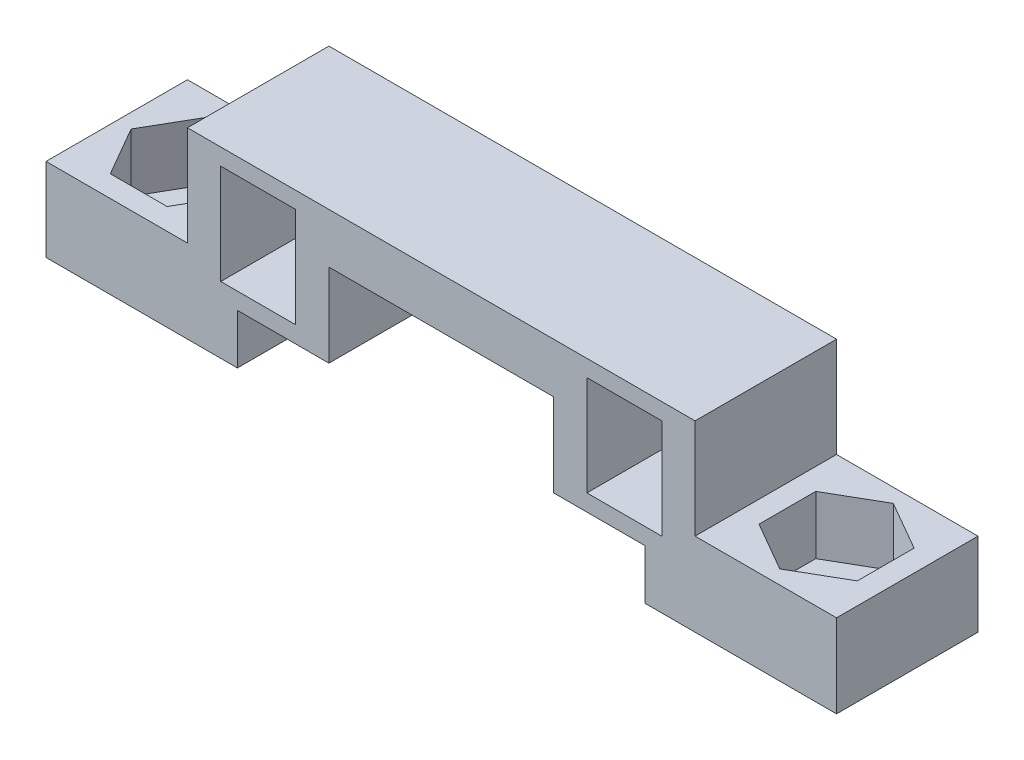
SolidWorks part; units mm, degrees
ref_plane "Front Plane" through (0, 0, 0) normal (0, 0, 1) x (1, 0, 0)
ref_plane "Top Plane" through (0, 0, 0) normal (0, 1, 0) x (1, 0, 0)
ref_plane "Right Plane" through (0, 0, 0) normal (1, 0, 0) x (0, 0, -1)
sketch "Sketch1" plane through (0, 0, 0) normal (0, 1, 0) x (1, 0, 0)
  line L1 (0, 0) -> (8.5, 0)
  line L2 (0, 0) -> (0, 8.5)
  line L3 (0, 8.5) -> (8.5, 8.5)
  line L4 (8.5, 0) -> (8.5, 8.5)
  line L5 (5.9855, 7.196) -> (2.5755, 7.196)
  line L6 (2.5755, 7.196) -> (0.8705, 4.2428)
  line L7 (0.8705, 4.2428) -> (2.5755, 1.2897)
  line L8 (2.5755, 1.2897) -> (5.9855, 1.2897)
  line L9 (5.9855, 1.2897) -> (7.6905, 4.2428)
  line L10 (7.6905, 4.2428) -> (5.9855, 7.196)
  circle A0 centre (4.2805, 4.2428) radius 2.9531 construction
  dimension "D1" = 8.5
  dimension "D2" = 8.5
  dimension "D3" = 3.41
extrude "Boss-Extrude1" add sketch "Sketch1" along normal blind 3.5
sketch "Sketch2" plane through (0, 0, 0) normal (0, -1, 0) x (1, 0, 0)
  line L1 (0, 0) -> (8.5, 0)
  line L2 (0, 0) -> (0, -8.5)
  line L3 (0, -8.5) -> (8.5, -8.5)
  line L4 (8.5, 0) -> (8.5, -8.5)
  circle A0 centre (4.25, -4.25) radius 1.5
  dimension "D1" = 3
extrude "Boss-Extrude2" add sketch "Sketch2" along normal blind 1.5
sketch "Sketch3" plane through (8.5, 0, 0) normal (1, 0, 0) x (0, 0, -1)
  line L1 (0, 3.5) -> (8.5, 3.5)
  line L2 (0, 3.5) -> (0, -1.5)
  line L3 (0, -1.5) -> (8.5, -1.5)
  line L4 (8.5, 3.5) -> (8.5, -1.5)
extrude "Boss-Extrude3" add sketch "Sketch3" along normal blind 3
sketch "Sketch4" plane through (0, 3.5, 0) normal (0, 1, 0) x (1, 0, 0)
  line L0 (0, 0) -> (11.5, 0) construction
  line L1 (11.5, 8.5) -> (8.5, 8.5)
  line L2 (11.5, 8.5) -> (11.5, 0)
  line L3 (11.5, 0) -> (8.5, 0)
  line L4 (8.5, 8.5) -> (8.5, 0)
  dimension "D1" = 3
extrude "Boss-Extrude4" add sketch "Sketch4" along normal blind 6
sketch "Sketch5" plane through (11.5, 0, 0) normal (1, 0, 0) x (0, 0, -1)
  line L0 (8.5, -1.5) -> (8.5, 9.5) construction
  line L1 (0, 9.5) -> (8.5, 9.5)
  line L2 (0, 9.5) -> (0, 6.5)
  line L3 (0, 6.5) -> (8.5, 6.5)
  line L4 (8.5, 9.5) -> (8.5, 6.5)
  dimension "D1" = 3
extrude "Boss-Extrude5" add sketch "Sketch5" along normal blind 27.5
sketch "Sketch6" plane through (0, 6.5, 0) normal (0, -1, 0) x (1, 0, 0)
  line L0 (39, -8.5) -> (11.5, -8.5) construction
  line L1 (39, 0) -> (36, 0)
  line L2 (39, 0) -> (39, -8.5)
  line L3 (39, -8.5) -> (36, -8.5)
  line L4 (36, 0) -> (36, -8.5)
  dimension "D1" = 3
extrude "Boss-Extrude6" add sketch "Sketch6" along normal up to surface (8 mm away) up to face at (5.75, -1.5, -4.25)
sketch "Sketch7" plane through (39, 0, 0) normal (1, 0, 0) x (0, 0, -1)
  line L0 (8.5, -1.5) -> (8.5, 9.5) construction
  line L1 (0, -1.5) -> (8.5, -1.5)
  line L2 (0, -1.5) -> (0, 3.5)
  line L3 (0, 3.5) -> (8.5, 3.5)
  line L4 (8.5, -1.5) -> (8.5, 3.5)
  dimension "D1" = 5
extrude "Boss-Extrude7" add sketch "Sketch7" along normal blind 8.5
sketch "Sketch8" plane through (0, 3.5, 0) normal (0, 1, 0) x (1, 0, 0)
  line L0 (39, 8.5) -> (39, 0) construction
  line L1 (46.2031, 5.955) -> (43.25, 7.66)
  line L2 (43.25, 7.66) -> (40.2969, 5.955)
  line L3 (40.2969, 5.955) -> (40.2969, 2.545)
  line L4 (40.2969, 2.545) -> (43.25, 0.84)
  line L5 (43.25, 0.84) -> (46.2031, 2.545)
  line L6 (46.2031, 2.545) -> (46.2031, 5.955)
  line L11 (47.5, 4.25) -> (39, 4.25) construction
  line L12 (47.5, 8.5) -> (47.5, 0) construction
  line L13 (43.25, 0) -> (43.25, 8.5) construction
  line L14 (47.5, 0) -> (39, 0) construction
  line L15 (47.5, 8.5) -> (39, 8.5) construction
  circle A0 centre (43.25, 4.25) radius 2.9531 construction
  dimension "D1" = 3.41
  dimension "D2" = 0
  dimension "D3" = 0
extrude "Cut-Extrude1" cut sketch "Sketch8" against normal blind 3.5
sketch "Sketch9" plane through (0, 0, 0) normal (0, 1, 0) x (1, 0, 0)
  line L0 (40.2969, 4.25) -> (46.2031, 4.25) construction
  line L1 (40.2969, 5.955) -> (40.2969, 2.545) construction
  line L2 (46.2031, 2.545) -> (46.2031, 5.955) construction
  circle A0 centre (34.75, 4.25) radius 1.5
  dimension "D1" = 3
sketch "Sketch10" plane through (0, 0, 0) normal (0, 1, 0) x (1, 0, 0)
  line L0 (40.2969, 4.25) -> (46.2031, 4.25) construction
  circle A0 centre (43.25, 4.25) radius 1.5
  dimension "3" = 3
extrude "Cut-Extrude3" cut sketch "Sketch10" against normal blind 3.5
sketch "Sketch11" plane through (8.5, 0, 0) normal (-1, 0, 0) x (0, 0, 1)
  line L0 (-4.25, 9.5) -> (-4.25, 3.5) construction
  line L1 (-8.5, 9.5) -> (0, 9.5) construction
  line L2 (-8.5, 3.5) -> (0, 3.5) construction
  line L3 (-8.5, 6.5) -> (0, 6.5) construction
  line L4 (-8.5, 9.5) -> (-8.5, 3.5) construction
  line L5 (0, 9.5) -> (0, 3.5) construction
  line L7 (-7.25, 4.25) -> (-1.25, 4.25)
  line L8 (-7.25, 4.25) -> (-7.25, 8.75)
  line L9 (-7.25, 8.75) -> (-1.25, 8.75)
  line L10 (-1.25, 4.25) -> (-1.25, 8.75)
  line L11 (-7.25, 4.25) -> (-1.25, 8.75) construction
  line L12 (-7.25, 8.75) -> (-1.25, 4.25) construction
  point P12 (-4.25, 6.5)
  dimension "D1" = 6
  dimension "D2" = 4.5
sketch "Sketch12" plane through (0, 9.5, 0) normal (0, 1, 0) x (1, 0, 0)
  line L0 (8.5, 4.25) -> (39, 4.25) construction
  line L1 (8.5, 8.5) -> (8.5, 0) construction
  line L2 (39, 8.5) -> (39, 0) construction
  line L3 (8.5, 8.5) -> (8.5, 0) construction
  line L4 (10.5, 1.25) -> (15, 1.25)
  line L5 (10.5, 1.25) -> (10.5, 7.25)
  line L6 (10.5, 7.25) -> (15, 7.25)
  line L7 (15, 1.25) -> (15, 7.25)
  line L8 (10.5, 1.25) -> (15, 7.25) construction
  line L9 (10.5, 7.25) -> (15, 1.25) construction
  point P6 (12.75, 4.25)
  dimension "D1" = 4.5
  dimension "D2" = 6
  dimension "D3" = 2
sketch "Sketch13" plane through (39, 0, 0) normal (1, 0, 0) x (0, 0, -1)
  line L0 (4.25, 9.5) -> (4.25, 3.5) construction
  line L1 (8.5, 9.5) -> (0, 9.5) construction
  line L2 (8.5, 3.5) -> (0, 3.5) construction
  line L3 (0, 6.5) -> (8.5, 6.5) construction
  line L4 (0, 9.5) -> (0, 3.5) construction
  line L6 (1.25, 4.25) -> (7.25, 4.25)
  line L7 (1.25, 4.25) -> (1.25, 8.75)
  line L8 (1.25, 8.75) -> (7.25, 8.75)
  line L9 (7.25, 4.25) -> (7.25, 8.75)
  line L10 (1.25, 4.25) -> (7.25, 8.75) construction
  line L11 (1.25, 8.75) -> (7.25, 4.25) construction
  point P11 (4.25, 6.5)
  dimension "D1" = 6
  dimension "D2" = 4.5
sketch "Sketch14" plane through (0, 9.5, 0) normal (0, 1, 0) x (1, 0, 0)
  line L0 (8.5, 4.25) -> (39, 4.25) construction
  line L1 (8.5, 8.5) -> (8.5, 0) construction
  line L2 (39, 8.5) -> (39, 0) construction
  line L4 (32.5, 1.25) -> (37, 1.25)
  line L5 (32.5, 1.25) -> (32.5, 7.25)
  line L6 (32.5, 7.25) -> (37, 7.25)
  line L7 (37, 1.25) -> (37, 7.25)
  line L8 (32.5, 1.25) -> (37, 7.25) construction
  line L9 (32.5, 7.25) -> (37, 1.25) construction
  point P6 (34.75, 4.25)
  dimension "D1" = 6
  dimension "D2" = 4.5
  dimension "D3" = 2
sketch "Sketch15" plane through (11.5, 0, 0) normal (1, 0, 0) x (0, 0, -1)
  line L0 (8.5, -1.5) -> (8.5, 6.5) construction
  line L1 (0, 6.5) -> (8.5, 6.5)
  line L2 (0, 6.5) -> (0, 1.5)
  line L3 (0, 1.5) -> (8.5, 1.5)
  line L4 (8.5, 6.5) -> (8.5, 1.5)
  dimension "D1" = 5
extrude "Boss-Extrude8" add sketch "Sketch15" along normal up to next
sketch "Sketch16" plane through (0, 0, 0) normal (0, 0, 1) x (1, 0, 0)
  line L0 (10.5, 9.5) -> (15, 9.5) construction
  line L1 (10.5, 2.5) -> (15, 2.5)
  line L2 (10.5, 2.5) -> (10.5, 8.5)
  line L3 (10.5, 8.5) -> (15, 8.5)
  line L4 (15, 2.5) -> (15, 8.5)
  line L5 (10.5, 2.5) -> (15, 8.5) construction
  line L6 (10.5, 8.5) -> (15, 2.5) construction
  line L7 (8.5, 4.25) -> (8.5, 8.75) construction
  line L8 (23.75, 9.5) -> (23.75, 1.5) construction
  line L9 (8.5, 9.5) -> (39, 9.5) construction
  line L10 (36, 1.5) -> (11.5, 1.5) construction
  line L11 (37, 8.5) -> (32.5, 8.5)
  line L12 (32.5, 2.5) -> (32.5, 8.5)
  line L13 (37, 2.5) -> (32.5, 2.5)
  line L14 (37, 2.5) -> (37, 8.5)
  point P0 (12.75, 5.5)
  dimension "D1" = 6
  dimension "D2" = 4.5
  dimension "D3" = 1
  dimension "D4" = 2
extrude "Cut-Extrude4" cut sketch "Sketch16" against normal blind 10
sketch "Sketch17" plane through (0, 0, 0) normal (0, 0, 1) x (1, 0, 0)
  line L8 (36, 1.5) -> (11.5, 1.5) construction
  line L9 (17, 1.5) -> (30.5, 1.5)
  line L10 (17, 1.5) -> (17, 6.5)
  line L11 (17, 6.5) -> (30.5, 6.5)
  line L12 (30.5, 1.5) -> (30.5, 6.5)
  line L13 (15, 2.5) -> (15, 8.5) construction
  line L14 (32.5, 8.5) -> (32.5, 2.5) construction
  line L15 (8.5, 9.5) -> (39, 9.5) construction
  dimension "D1" = 2
  dimension "D2" = 2
  dimension "D3" = 3
extrude "Cut-Extrude5" cut sketch "Sketch17" against normal blind 10
